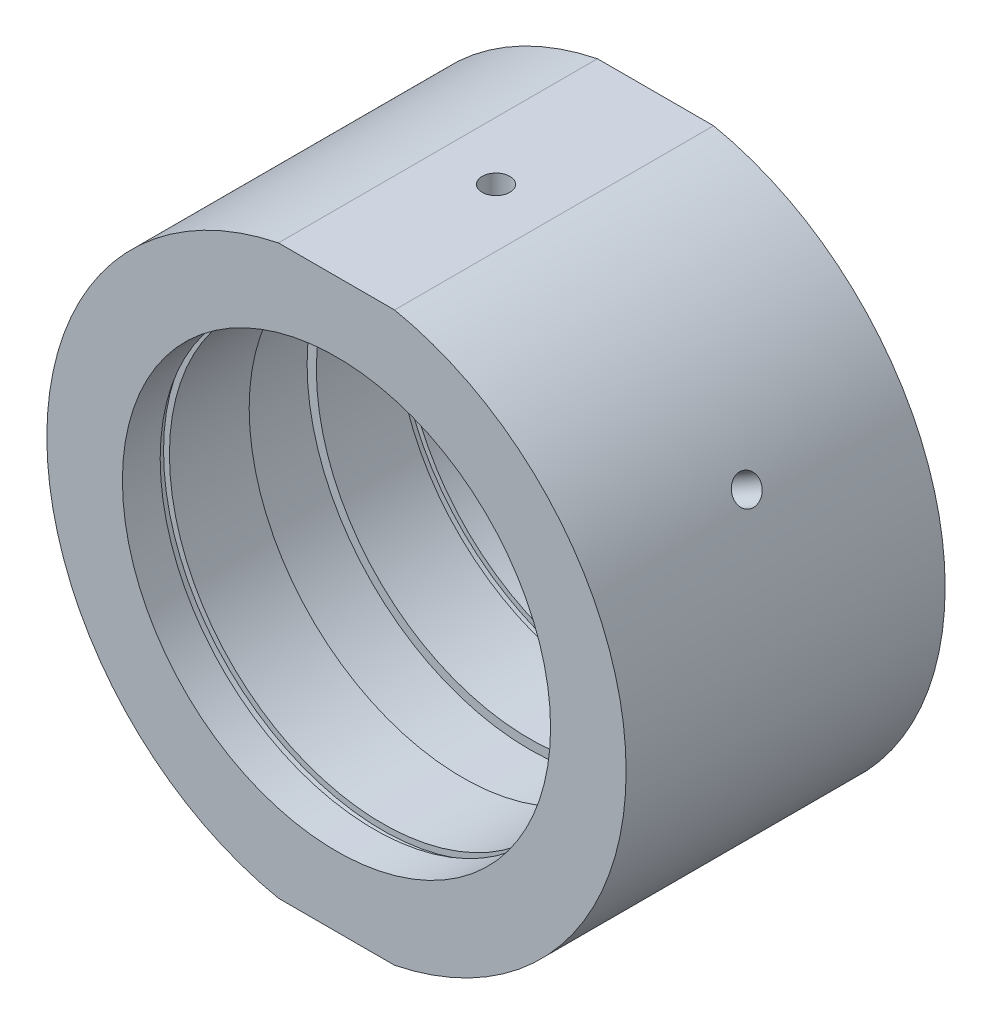
SolidWorks part; units mm, degrees
ref_plane "前视基准面" through (0, 0, 0) normal (0, 0, 1) x (1, 0, 0)
ref_plane "上视基准面" through (0, 0, 0) normal (0, 1, 0) x (1, 0, 0)
ref_plane "右视基准面" through (0, 0, 0) normal (1, 0, 0) x (0, 0, -1)
sketch "草图1" plane through (0, 0, 0) normal (0, 1, 0) x (1, 0, 0)
  line L0 (0, 31.9391) -> (0, -26.491) construction
  line L1 (34.5, 19) -> (34.5, -19)
  line L2 (34.5, -19) -> (25.5, -19)
  line L3 (25.5, -19) -> (25.5, -14.5)
  line L4 (25.5, -14.5) -> (26.1, -14.5)
  line L5 (26.1, -14.5) -> (26.1, -13.5)
  line L6 (26.1, -13.5) -> (25.4, -13.5)
  line L7 (25.4, -13.5) -> (25.4, -4)
  line L8 (25.4, -4) -> (26.5, -4)
  line L9 (26.5, -4) -> (26.5, 4)
  line L10 (26.5, 4) -> (25.4, 4)
  line L11 (25.4, 4) -> (25.4, 13.5)
  line L12 (25.4, 13.5) -> (26.1, 13.5)
  line L13 (26.1, 13.5) -> (26.1, 14.5)
  line L14 (26.1, 14.5) -> (25.5, 14.5)
  line L15 (25.5, 14.5) -> (25.5, 19)
  line L16 (25.5, 19) -> (34.5, 19)
  line L17 (34.5, 0) -> (-5.0345, 0) construction
  point P6 (26.5, 0)
  dimension "D1" = 38
  dimension "D2" = 26.5
  dimension "D3" = 25.4
  dimension "D4" = 25.4
  dimension "D5" = 26.1
  dimension "D6" = 26.1
  dimension "D7" = 25.5
  dimension "D8" = 25.5
  dimension "D9" = 34.5
  dimension "D10" = 1
  dimension "D11" = 1
  dimension "D12" = 5.5
  dimension "D13" = 5.5
  dimension "D14" = 8
  dimension "D15" = 4
  dimension "D16" = 19
  dimension "D17" = 15
  dimension "D18" = 0
revolve "旋转1" add sketch "草图1" angle 360 about L0
cosmetic thread "装饰螺纹线4" parameters "D1"=4.4999, "D2"=52
cosmetic thread "装饰螺纹线5" parameters "D1"=8, "D2"=52
sketch "草图2" plane through (0, 0, 19) normal (0, 0, 1) x (1, 0, 0)
  line L0 (0, 0) -> (43.1523, 0) construction
  line L1 (-33.152, 43.0489) -> (30.8698, 43.0489)
  line L2 (-33.152, 43.0489) -> (-33.152, 33.8)
  line L3 (-33.152, 33.8) -> (30.8698, 33.8)
  line L4 (30.8698, 43.0489) -> (30.8698, 33.8)
  line L5 (30.8698, -43.0489) -> (30.8698, -33.8)
  line L6 (-33.152, -33.8) -> (30.8698, -33.8)
  line L7 (-33.152, -43.0489) -> (-33.152, -33.8)
  line L8 (-33.152, -43.0489) -> (30.8698, -43.0489)
  circle A1 centre (0, 0) radius 34.5 construction
  dimension "D1" = 33.8
  dimension "D2" = 0.7
extrude "切除-拉伸1" cut sketch "草图2" against normal blind 49
sketch "草图10" plane through (0, 0, 0) normal (0, 0, 1) x (1, 0, 0)
  line L0 (0, 33.8) -> (0, -33.8)
  line L1 (6.9145, 33.8) -> (-6.9145, 33.8) construction
  line L2 (-6.9145, -33.8) -> (6.9145, -33.8) construction
  line L3 (0, 0) -> (-29.8779, 17.25)
  line L4 (0, 0) -> (29.8779, 17.25)
  line L5 (6.9145, 33.8) -> (0, 33.8)
  line L6 (0, -33.8) -> (3.1773, -33.8)
  arc A0 (-6.9145, 33.8) -> (-6.9145, -33.8) centre (0, 0) ccw construction
  arc A1 (6.9145, -33.8) -> (6.9145, 33.8) centre (0, 0) ccw construction
  arc A2 (-6.9145, 33.8) -> (-29.8779, 17.25) centre (0, 0) ccw
  arc A3 (29.8779, 17.25) -> (6.9145, 33.8) centre (0, 0) ccw
  dimension "D1" = 60
  dimension "D2" = 60
hole_wizard "M4 螺纹孔2" positions "草图15" profile "草图16" tap size "M4" standard "ISO"
sketch "草图15" plane through (0, 33.8, 0) normal (0, 1, 0) x (1, 0, 0)
  point P0 (0, 0)
sketch "草图16" plane through (0, 33.8, 0) normal (1, 0, 0) x (0, 0, 1)
  line L0 (0, 0) -> (0, 6.4914)
  line L1 (0, 6.4914) -> (1.65, 5.5)
  line L2 (1.65, 5.5) -> (1.65, 0)
  line L5 (1.65, 0) -> (0, 0)
  line L10 (0, 6.4914) -> (-1.65, 5.5) construction
  line L11 (0, -6.35) -> (0, 107.95) construction
  dimension "螺纹孔钻头直径" = 3.3
  dimension "螺纹孔钻头深度" = 5.5
  dimension "导头角度" = 118
cosmetic thread "孔螺蚊线3" parameters "D1"=5.5, "D2"=4
hole_wizard "M6 螺纹孔2" positions "草图17" profile "草图18" tap size "M6" standard "ISO"
sketch "草图17" plane through (0, -33.8, 0) normal (0, -1, 0) x (-1, 0, 0)
  point P0 (0, 0)
sketch "草图18" plane through (0, -33.8, 0) normal (1, 0, 0) x (0, 0, -1)
  line L0 (0, 0) -> (0, 7.0022)
  line L1 (0, 7.0022) -> (2.5, 5.5)
  line L2 (2.5, 5.5) -> (2.5, 0)
  line L5 (2.5, 0) -> (0, 0)
  line L10 (0, 7.0022) -> (-2.5, 5.5) construction
  line L11 (0, -6.35) -> (0, 107.95) construction
  dimension "螺纹孔钻头直径" = 5
  dimension "螺纹孔钻头深度" = 5.5
  dimension "导头角度" = 118
cosmetic thread "孔螺蚊线4" parameters "D1"=5.5, "D2"=6
hole_wizard "M4 螺纹孔3" positions "3D草图10" profile "草图19" tap size "M4" standard "ISO"
sketch3d "3D草图10"
  point P0 (29.8779, 17.25, 0)
  point P3 (-29.8779, 17.25, 0)
  point P6 (-29.8779, 17.25, 0)
  point P8 (-29.8779, 17.25, 0)
  point P12 (29.8779, 17.25, 0)
  point P15 (29.8779, 17.25, 0)
  point P18 (29.8779, 17.25, 0)
cosmetic thread "孔螺蚊线5" parameters "D1"=8, "D2"=4
sketch "草图19" plane through (29.8779, 17.25, 0) normal (0, 0, 1) x (-0.5, 0.866, 0)
  line L0 (0, 0) -> (0, 11.0914)
  line L1 (0, 11.0914) -> (1.65, 10.1)
  line L2 (1.65, 10.1) -> (1.65, 0)
  line L5 (1.65, 0) -> (0, 0)
  line L10 (0, 11.0914) -> (-1.65, 10.1) construction
  line L11 (0, -6.35) -> (0, 107.95) construction
  dimension "螺纹孔钻头直径" = 3.3
  dimension "螺纹孔钻头深度" = 10.1
  dimension "导头角度" = 118
cosmetic thread "孔螺蚊线6" parameters "D1"=8, "D2"=4
